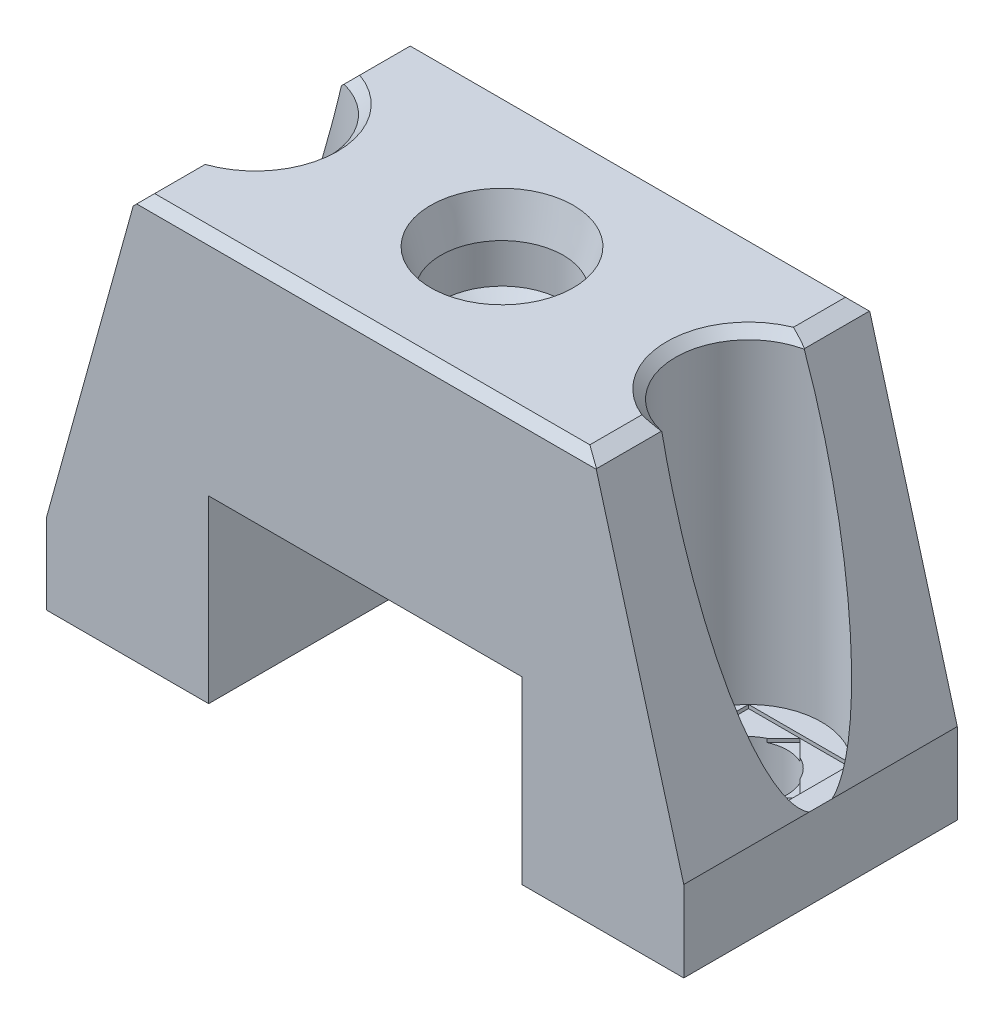
SolidWorks part; units mm, degrees
ref_plane "Front Plane" through (0, 0, 0) normal (0, 0, 1) x (1, 0, 0)
ref_plane "Top Plane" through (0, 0, 0) normal (0, 1, 0) x (1, 0, 0)
ref_plane "Right Plane" through (0, 0, 0) normal (1, 0, 0) x (0, 0, -1)
sketch "Sketch1" plane through (0, 0, 0) normal (0, 0, 1) x (1, 0, 0)
  line L0 (0, 0) -> (0, 12.1773) construction
  line L1 (3.15, 0.7051) -> (2.5, 0.25)
  line L2 (2.5, 0.25) -> (3.3881, 0.25) construction
  line L3 (2.5, 0) -> (2.5, 0.25)
  line L4 (2.5, 0) -> (6.5, 0)
  line L5 (3.15, 0.7051) -> (3.15, 2.55)
  line L6 (3.15, 2.55) -> (1.7, 2.55)
  line L7 (1.7, 2.55) -> (1.7, 6.05)
  line L8 (6.5, 0) -> (6.5, 11.55)
  line L10 (1.7, 6.05) -> (3.4, 7.2404)
  line L12 (3.9674, 11.55) -> (6.5, 11.55)
  line L13 (1.7, 6.05) -> (4.0603, 6.05) construction
  line L14 (3.4, 7.2404) -> (3.4, 9.4325)
  line L15 (3.4, 9.4325) -> (3.9674, 11.55)
  circle A0 centre (2.34, 1.9029) radius 0.89 construction
  dimension "D1" = 1.78
  dimension "D2" = 2.9
  dimension "D3" = 2.3
  dimension "D4" = 6.3
  dimension "D5" = 35
  dimension "D6" = 0.25
  dimension "D7" = 6.8
  dimension "D8" = 5.5
  dimension "D9" = 35
  dimension "D10" = 5
  dimension "D11" = 3.4
  dimension "D12" = 3.5
  dimension "D13" = 13
  dimension "D14" = 15
revolve "Revolve1" add sketch "Sketch1" angle 360 about L0
sketch "Sketch3" plane through (0, 0, 0) normal (0, -1, 0) x (1, 0, 0)
  line L1 (-7.7, -6.6) -> (7.7, -6.6) construction
  line L2 (-7.7, -6.6) -> (-7.7, 6.6) construction
  line L3 (-7.7, 6.6) -> (7.7, 6.6) construction
  line L4 (7.7, -6.6) -> (7.7, 6.6) construction
  line L5 (-7.7, -6.6) -> (7.7, 6.6) construction
  line L6 (-7.7, 6.6) -> (7.7, -6.6) construction
  line L11 (-17.7, 7.6) -> (17.7, 7.6)
  line L12 (0, 0) -> (0, 14.9234) construction
  line L14 (17.7, -7.6) -> (-17.7, -7.6)
  line L23 (-17.7, 7.6) -> (-17.7, -7.6)
  line L24 (17.7, 7.6) -> (17.7, -7.6)
  circle A2 centre (13.7, 0) radius 2.15
  circle A9 centre (-13.7, 0) radius 2.15
  circle A13 centre (0, 0) radius 6.5
  circle A14 centre (0, 0) radius 6.5 construction
  point P0 (0, 0)
  point P8 (17.7, 0)
  dimension "D4" = 4.3
  dimension "D5" = 4
  dimension "D1" = 13.2
  dimension "D2" = 15.4
  dimension "D6" = 27.4
  dimension "D3" = 1
extrude "Boss-Extrude1" add sketch "Sketch3" against normal up to surface (11.55 mm away) up to face at (0, 11.55, -3.9674)
sketch "Sketch4" plane through (0, 0, 0) normal (0, -1, 0) x (1, 0, 0)
  line L0 (-7.7, -6.6) -> (-7.7, 6.6)
  line L1 (-8.7, -7.6) -> (8.7, -7.6)
  line L2 (-8.7, -7.6) -> (-8.7, 7.6)
  line L3 (-8.7, 7.6) -> (8.7, 7.6)
  line L4 (8.7, -7.6) -> (8.7, 7.6)
  line L5 (-8.7, -7.6) -> (8.7, 7.6) construction
  line L6 (-8.7, 7.6) -> (8.7, -7.6) construction
  line L7 (-7.7, 6.6) -> (7.7, 6.6)
  line L8 (7.7, -6.6) -> (7.7, 6.6)
  line L9 (-7.7, -6.6) -> (7.7, -6.6)
  point P0 (0, 0)
  dimension "D2" = 15.4
  dimension "D3" = 13.2
  dimension "D1" = 1
extrude "Boss-Extrude2" add sketch "Sketch4" along normal blind 1
sketch "Sketch5" plane through (0, 0, 0) normal (0, -1, 0) x (1, 0, 0)
  line L32 (8.7, 7.6) -> (8.7, -7.6) construction
  line L33 (8.7, -7.6) -> (17.7, -7.6) construction
  line L34 (17.7, -7.6) -> (17.7, 7.6) construction
  line L35 (17.7, 7.6) -> (8.7, 7.6) construction
  line L36 (-8.7, -7.6) -> (-8.7, 7.6) construction
  line L37 (-8.7, 7.6) -> (-17.7, 7.6) construction
  line L38 (-17.7, 7.6) -> (-17.7, -7.6) construction
  line L39 (-17.7, -7.6) -> (-8.7, -7.6) construction
  line L40 (8.7, 7.6) -> (8.7, -7.6)
  line L41 (8.7, -7.6) -> (17.7, -7.6)
  line L42 (17.7, -7.6) -> (17.7, 7.6)
  line L43 (17.7, 7.6) -> (8.7, 7.6)
  line L44 (-8.7, -7.6) -> (-8.7, 7.6)
  line L45 (-8.7, 7.6) -> (-17.7, 7.6)
  line L46 (-17.7, 7.6) -> (-17.7, -7.6)
  line L47 (-17.7, -7.6) -> (-8.7, -7.6)
  circle A6 centre (13.7, 0) radius 2.15 construction
  circle A7 centre (-13.7, 0) radius 2.15 construction
  circle A16 centre (13.7, 0) radius 2.15
  circle A17 centre (-13.7, 0) radius 2.15
  point P4 (16.5284, -2.8284)
extrude "Boss-Extrude3" add sketch "Sketch5" along normal blind 11.5
sketch "Sketch6" plane through (0, 11.55, 0) normal (0, 1, 0) x (1, 0, 0)
  line L12 (0, 0) -> (0, 4.7404) construction
  circle A6 centre (-13.7, 0) radius 4.05
  circle A7 centre (13.7, 0) radius 4.05
  dimension "D1" = 8.1
extrude "Cut-Extrude1" cut sketch "Sketch6" against normal offset from surface (18.05 mm away) 5
sketch "Sketch8" plane through (0, 0, -7.6) normal (0, 0, -1) x (-1, 0, 0)
  line L0 (-17.7, -6.5) -> (-12.7, 11.55)
  line L1 (-17.7, 11.55) -> (-17.7, -11.5) construction
  line L2 (17.7, 11.55) -> (-17.7, 11.55) construction
  line L3 (-12.7, 11.55) -> (-17.7, 11.55)
  line L4 (-17.7, 11.55) -> (-17.7, -6.5)
  line L5 (0, 0) -> (0, 8.1966) construction
  line L6 (17.7, 11.55) -> (17.7, -6.5)
  line L7 (12.7, 11.55) -> (17.7, 11.55)
  line L8 (17.7, -6.5) -> (12.7, 11.55)
  dimension "D1" = 5
extrude "Cut-Extrude4" cut sketch "Sketch8" against normal through all
chamfer "Chamfer1" distance 0.5 angle 45 18 edges at (13.7, -11.5, -2.15) (17.7, -11.5, 0) (13.2, -11.5, -7.6) (8.7, -11.5, 0) (13.2, -11.5, 7.6) (-13.7, -11.5, -2.15) (-17.7, -11.5, 0) (-13.2, -11.5, 7.6) (-8.7, -11.5, 0) (-13.2, -11.5, -7.6) (-12.7, 11.55, 5.7623) (-9.65, 11.55, 0) (-12.7, 11.55, -5.7623) (0, 11.55, -7.6) (12.7, 11.55, -5.7623) (9.65, 11.55, 0) (12.7, 11.55, 5.7623) (0, 11.55, 7.6)
sketch "Sketch10" plane through (0, -6.5, 0) normal (0, 1, 0) x (1, 0, 0)
  line L0 (0, 0) -> (0, 5.8704) construction
  line L1 (-16.5638, 2.8638) -> (-10.8362, 2.8638)
  line L2 (-16.5638, 2.8638) -> (-16.5638, -2.8638)
  line L3 (-16.5638, -2.8638) -> (-10.8362, -2.8638)
  line L4 (-10.8362, 2.8638) -> (-10.8362, -2.8638)
  line L5 (10.8362, 2.8638) -> (10.8362, -2.8638)
  line L6 (16.5638, -2.8638) -> (10.8362, -2.8638)
  line L7 (16.5638, 2.8638) -> (16.5638, -2.8638)
  line L8 (16.5638, 2.8638) -> (10.8362, 2.8638)
  arc A0 (-17.7, -0.6344) -> (-17.7, 0.6344) centre (-13.7, 0) ccw construction
extrude "Cut-Extrude5" cut sketch "Sketch10" against normal blind 0.2
sketch "Sketch11" plane through (0, -6.7, 0) normal (0, 1, 0) x (1, 0, 0)
  line L0 (-16.5638, 0) -> (-13.7, -2.8638)
  line L1 (-16.5638, 0) -> (-13.7, 2.8638)
  line L2 (-13.7, -2.8638) -> (-10.8362, 0)
  line L3 (-13.7, 2.8638) -> (-10.8362, 0)
  line L4 (-16.5638, 0) -> (-10.8362, 0) construction
  line L5 (-13.7, -2.8638) -> (-13.7, 2.8638) construction
  line L6 (-10.8362, -2.8638) -> (-10.8362, 2.8638) construction
  line L7 (-16.5638, -2.8638) -> (-10.8362, -2.8638) construction
  line L8 (0, 0) -> (0, 5.3265) construction
  line L9 (13.7, 2.8638) -> (10.8362, 0)
  line L10 (13.7, -2.8638) -> (10.8362, 0)
  line L11 (16.5638, 0) -> (13.7, 2.8638)
  line L12 (16.5638, 0) -> (13.7, -2.8638)
  circle A0 centre (-13.7, 0) radius 2.15 construction
  point P1 (-13.7, 0)
  point P3 (13.7, 0)
extrude "Cut-Extrude6" cut sketch "Sketch11" against normal blind 0.2
